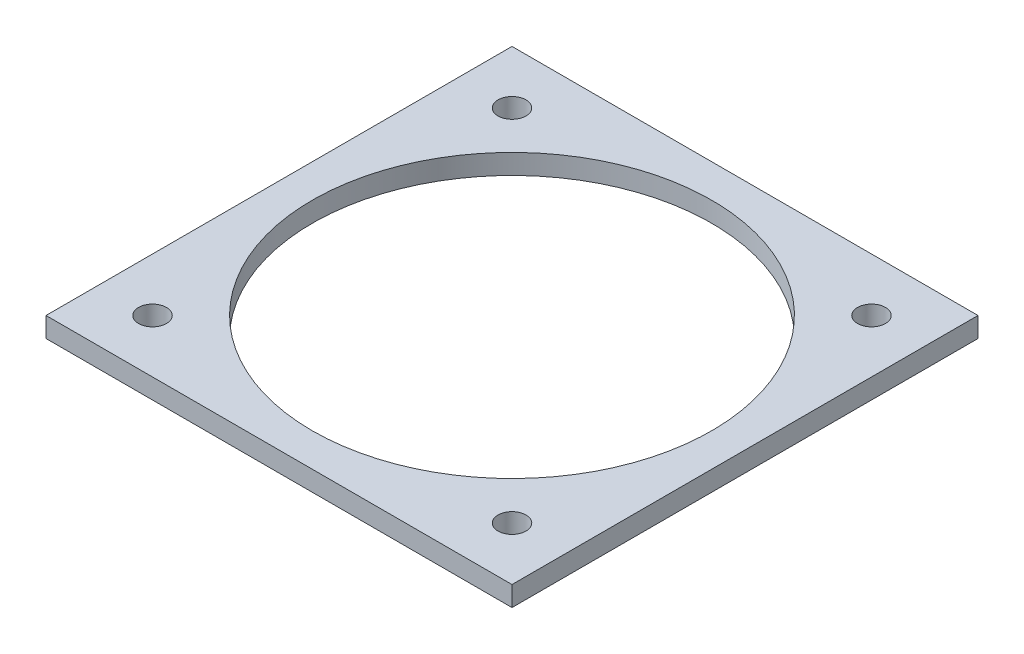
SolidWorks part; units mm, degrees
material "6061-T6 (SS)"
ref_plane "前视基准面" through (0, 0, 0) normal (0, 0, 1) x (1, 0, 0)
ref_plane "上视基准面" through (0, 0, 0) normal (0, 1, 0) x (1, 0, 0)
ref_plane "右视基准面" through (0, 0, 0) normal (1, 0, 0) x (0, 0, -1)
sketch "草图1" plane through (0, 0, 0) normal (0, 1, 0) x (1, 0, 0)
  line L1 (-35, -35) -> (35, -35)
  line L2 (-35, -35) -> (-35, 35)
  line L3 (-35, 35) -> (35, 35)
  line L4 (35, -35) -> (35, 35)
  line L5 (-35, -35) -> (35, 35) construction
  line L6 (-35, 35) -> (35, -35) construction
  circle A0 centre (0, 0) radius 30
  point P0 (0, 0)
  dimension "D3" = 60
  dimension "D1" = 70
  dimension "D2" = 70
extrude "凸台-拉伸1" add sketch "草图1" along normal blind 3
sketch "草图2" plane through (0, 3, 0) normal (0, 1, 0) x (1, 0, 0)
  line L0 (-35, -35) -> (35, 35) construction
  line L1 (35, 35) -> (-35, 35) construction
  circle A0 centre (27, 27) radius 2.1
  dimension "D1" = 4.2
  dimension "D2" = 8
extrude "切除-拉伸1" cut sketch "草图2" against normal blind 10
pattern_circular "阵列(圆周)1" count 4 over 360 about axis through (0, 0, 0) along (0, 1, 0) of "切除-拉伸1"
